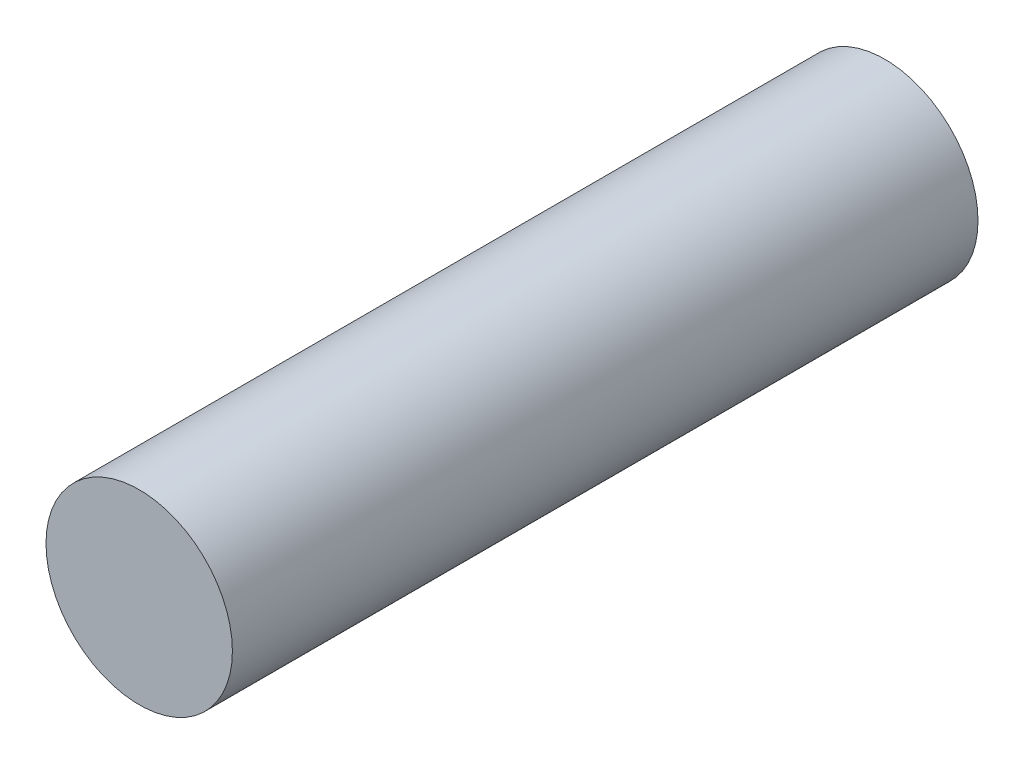
SolidWorks part; units mm, degrees
ref_plane "Front" through (0, 0, 0) normal (0, 0, 1) x (1, 0, 0)
ref_plane "Top" through (0, 0, 0) normal (0, 1, 0) x (1, 0, 0)
ref_plane "Right" through (0, 0, 0) normal (1, 0, 0) x (0, 0, -1)
sketch "Sketch1" plane through (0, 0, 0) normal (0, 0, 1) x (1, 0, 0)
  circle A0 centre (0, 0) radius 1
  dimension "D1" = 2
extrude "Base-Extrude" add sketch "Sketch1" along normal blind 8
